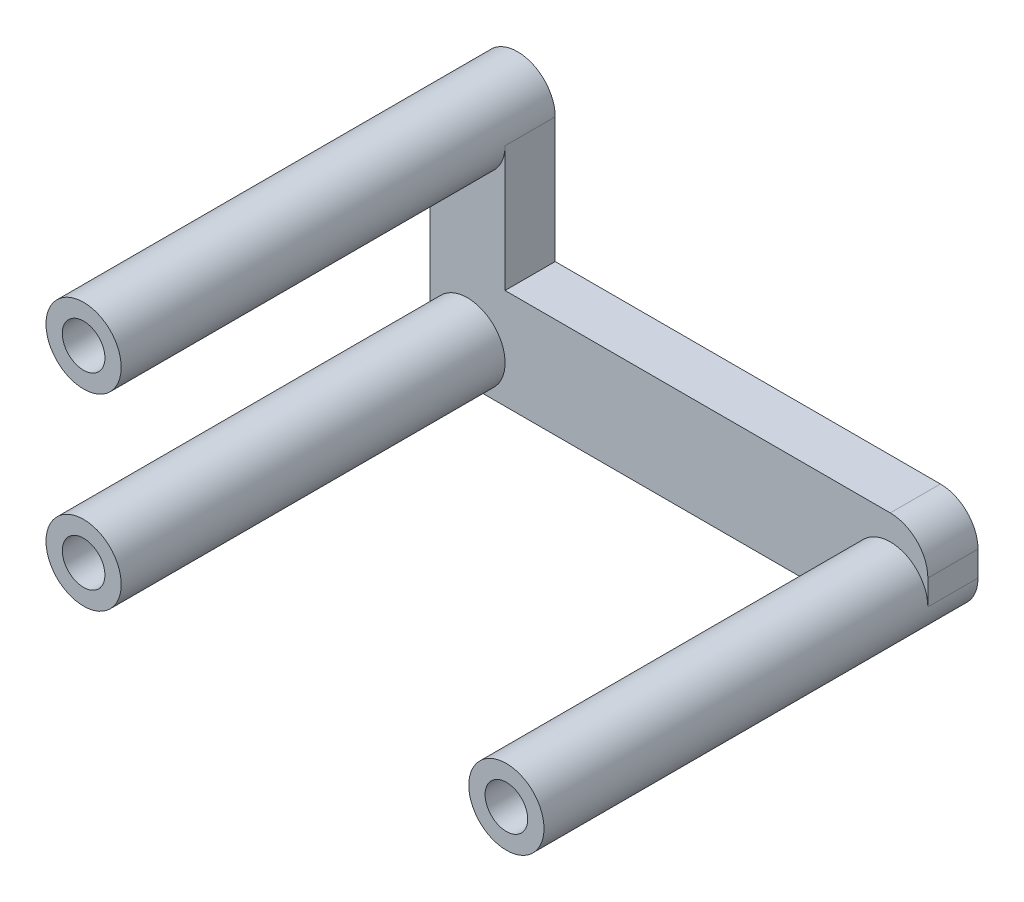
SolidWorks part; units mm, degrees
ref_plane "Ebene vorne" through (0, 0, 0) normal (0, 0, 1) x (1, 0, 0)
ref_plane "Ebene oben" through (0, 0, 0) normal (0, 1, 0) x (1, 0, 0)
ref_plane "Ebene rechts" through (0, 0, 0) normal (1, 0, 0) x (0, 0, -1)
sketch "Skizze1" plane through (0, 0, 0) normal (0, 0, 1) x (1, 0, 0)
  line L0 (-6.081, 22.2627) -> (-6.081, 18.161) construction
  circle A0 centre (-15.621, 18.161) radius 3
  circle A1 centre (3.459, 18.161) radius 3
  dimension "D1" = 6
extrude "Aufsatz-Linear austragen1" add sketch "Skizze1" along normal blind 4
sketch "Skizze2" plane through (0, 0, 0) normal (0, 0, 1) x (1, 0, 0)
  line L0 (-32.7334, 31.95) -> (-32.7334, 14.45) construction
  line L1 (9.9969, 21.161) -> (-29.7334, 21.161)
  line L2 (9.9969, 21.161) -> (9.9969, 15.161)
  line L3 (9.9969, 15.161) -> (-29.7334, 15.161)
  line L4 (-29.7334, 21.161) -> (-29.7334, 15.161)
  line L8 (12.9969, 16) -> (12.9969, 27) construction
  circle A1 centre (-15.621, 18.161) radius 3 construction
  circle A2 centre (3.459, 18.161) radius 3 construction
  dimension "D1" = 3
  dimension "D2" = 3
extrude "Aufsatz-Linear austragen2" add sketch "Skizze2" along normal blind 4 from offset 1
sketch "Skizze3" plane through (0, 0, 1) normal (0, 0, 1) x (1, 0, 0)
  line L0 (-29.7334, 21.161) -> (-29.7334, 15.161) construction
  line L1 (9.9969, 21.161) -> (-29.7334, 21.161) construction
  line L2 (-9.8683, 21.161) -> (-9.8683, 15.161) construction
  line L3 (-29.7334, 15.161) -> (9.9969, 15.161) construction
  line L4 (-32.8167, 25.661) -> (-21.8562, 25.661) construction
  circle A0 centre (-26.7334, 18.161) radius 3
  circle A2 centre (6.9969, 18.161) radius 3
  circle A3 centre (-26.7334, 33.161) radius 3
  dimension "D1" = 15
extrude "Aufsatz-Linear austragen3" add sketch "Skizze3" against normal up to surface (34.6252 mm away) from surface
sketch "Skizze5" plane through (0, 0, 5) normal (0, 0, 1) x (1, 0, 0)
  line L5 (-26.7334, 21.161) -> (-36.7578, 21.161)
  line L10 (-36.7578, 21.161) -> (-36.7578, 15.161)
  line L11 (-36.7578, 15.161) -> (-26.7334, 15.161)
  line L12 (-9.8683, 21.161) -> (-9.8683, 16.6542) construction
  line L13 (6.9969, 21.161) -> (-26.7334, 21.161) construction
  line L14 (17.0213, 15.161) -> (6.9969, 15.161)
  line L15 (17.0213, 21.161) -> (17.0213, 15.161)
  line L16 (6.9969, 21.161) -> (17.0213, 21.161)
  arc A3 (-26.7334, 21.161) -> (-26.7334, 15.161) centre (-26.7334, 18.161) ccw
  circle A5 centre (-26.7334, 18.161) radius 3 construction
  arc A6 (6.9969, 21.161) -> (6.9969, 15.161) centre (6.9969, 18.161) cw
  arc A7 (6.9969, 21.161) -> (6.9969, 15.161) centre (6.9969, 18.161) ccw construction
extrude "Schnitt-Linear austragen1" cut sketch "Skizze5" against normal through all
sketch "Skizze11" plane through (0, 0, 5) normal (0, 0, 1) x (1, 0, 0)
  line L9 (-23.7334, 33.161) -> (-29.7334, 33.161)
  line L10 (-23.7334, 33.161) -> (-23.7334, 18.161)
  line L11 (-23.7334, 18.161) -> (-29.7334, 18.161)
  line L12 (-29.7334, 33.161) -> (-29.7334, 18.161)
  circle A0 centre (-26.7334, 33.161) radius 3 construction
  arc A1 (-26.7334, 15.161) -> (-26.7334, 21.161) centre (-26.7334, 18.161) ccw construction
extrude "Aufsatz-Linear austragen8" add sketch "Skizze11" against normal up to surface (4 mm away) up to face at (-22.6772, 18.161, 1)
sketch "Skizze12" plane through (0, 0, 35.6252) normal (0, 0, 1) x (1, 0, 0)
  line L0 (-32.5598, 25.661) -> (-9.8683, 25.661) construction
  line L1 (-9.8683, 25.661) -> (-7.7074, 30.52) construction
  circle A0 centre (-26.7334, 33.161) radius 1.7
  circle A1 centre (-26.7334, 18.161) radius 1.7
  circle A2 centre (6.9969, 18.161) radius 1.7
  dimension "D1" = 3.4
extrude "Schnitt-Linear austragen6" cut sketch "Skizze12" against normal blind 4
sketch "Skizze14" plane through (0, 0, 1) normal (0, 0, -1) x (-1, 0, 0)
  line L0 (26.7334, 15.161) -> (15.621, 15.161) construction
  line L1 (-6.459, 21.161) -> (18.621, 21.161)
  line L2 (-6.459, 21.161) -> (-6.459, 15.161)
  line L3 (-6.459, 15.161) -> (18.621, 15.161)
  line L4 (18.621, 21.161) -> (18.621, 15.161)
  line L5 (-6.9969, 21.161) -> (-3.459, 21.161) construction
  arc A0 (-3.459, 21.161) -> (-3.459, 15.161) centre (-3.459, 18.161) ccw construction
  arc A1 (15.621, 15.161) -> (15.621, 21.161) centre (15.621, 18.161) ccw construction
extrude "Schnitt-Linear austragen8" cut sketch "Skizze14" along normal through all
sketch "Skizze15" plane through (0, 0, 1) normal (0, 0, -1) x (-1, 0, 0)
  line L0 (23.7334, 21.161) -> (23.7334, 33.161) construction
  line L1 (-9.9969, 18.161) -> (23.7334, 18.161)
  line L2 (-9.9969, 18.161) -> (-9.9969, 23.161)
  line L3 (-9.9969, 23.161) -> (23.7334, 23.161)
  line L4 (23.7334, 18.161) -> (23.7334, 23.161)
  line L5 (-6.9969, 21.161) -> (23.7334, 21.161) construction
  arc A0 (-6.9969, 21.161) -> (-6.9969, 15.161) centre (-6.9969, 18.161) ccw construction
  dimension "D1" = 2
extrude "Aufsatz-Linear austragen9" add sketch "Skizze15" against normal up to surface (4 mm away) up to face at (-17.0074, 22.5355, 5)
sketch "Skizze16" plane through (0, 0, 1) normal (0, 0, -1) x (-1, 0, 0)
  point P0 (15.621, 18.161)
  point P1 (-3.459, 18.161)
sketch "Skizze17" plane through (0, 0, 1) normal (0, 0, -1) x (-1, 0, 0)
  line L0 (-3.459, 18.161) -> (-3.459, 18.5311) construction
  line L1 (-5.459, 20.161) -> (15.621, 20.161) construction
  line L2 (15.621, 20.161) -> (15.621, 18.161) construction
  circle A0 centre (-5.459, 20.161) radius 1.7
  circle A1 centre (15.621, 20.161) radius 1.7
  dimension "D3" = 3.4
  dimension "D4" = 3.4
  dimension "D1" = 2
  dimension "D2" = 2
extrude "Schnitt-Linear austragen9" cut sketch "Skizze17" against normal blind 2
fillet "Verrundung1" radius 3 1 edges at (9.9969, 23.161, 3)
equation "\"M2EinschmelzGewindeDurchmesser\"=3.4"
equation "\"M2EinschmelzGewindeTiefe\"= 4.0"
equation "\"M3EinschmelzGewindeDurchmesser\"= 4.2"
equation "\"M3EinschmelzGewindeTief\"= 5.7"
equation "\"M2SchraubeLoch\"=2.3"
equation "\"M3SchraubeLoch\"=3.3"
equation "\"offSetVonGummiReifen\"= 3.0"
equation "\"D1@Skizze12\"=\"M2EinschmelzGewindeDurchmesser\""
equation "\"D1@Schnitt-Linear austragen6\"=\"M2EinschmelzGewindeTiefe\""
equation "\"D1\"= \"M2EinschmelzGewindeTiefe\""
equation "\"D3@Skizze17\"=\"M2EinschmelzGewindeDurchmesser\""
equation "\"D4@Skizze17\"=\"M2EinschmelzGewindeDurchmesser\""
